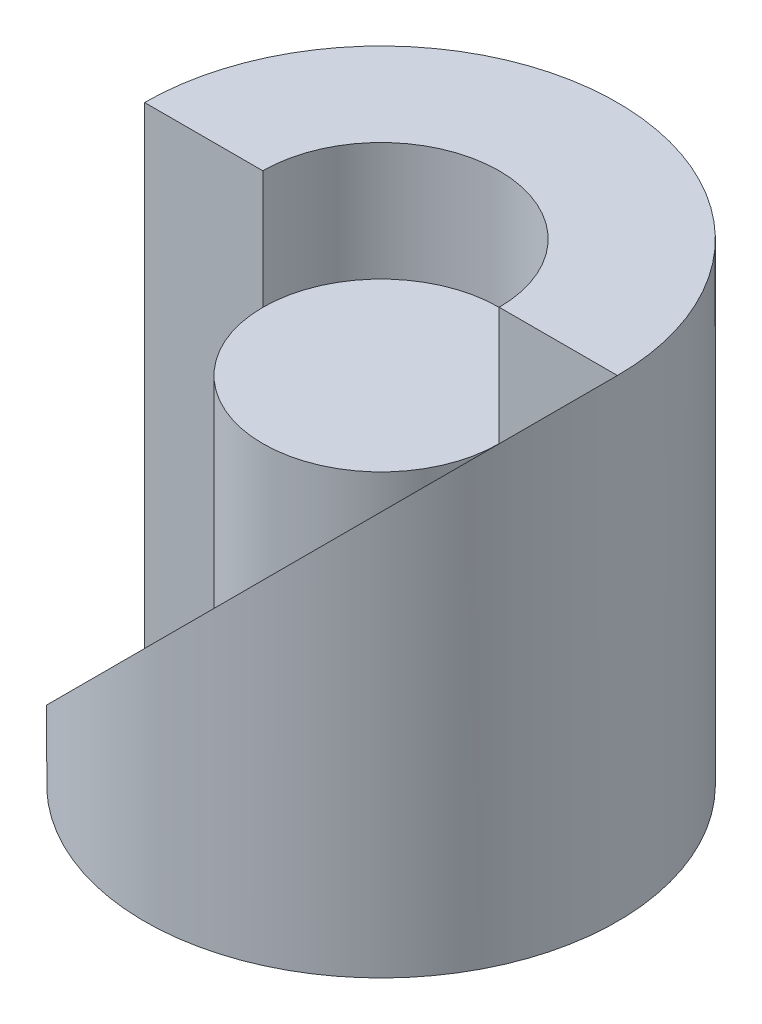
SolidWorks part; units mm, degrees
ref_plane "Front Plane" through (0, 0, 0) normal (0, 0, 1) x (1, 0, 0)
ref_plane "Top Plane" through (0, 0, 0) normal (0, 1, 0) x (1, 0, 0)
ref_plane "Right Plane" through (0, 0, 0) normal (1, 0, 0) x (0, 0, -1)
sketch "Sketch1" plane through (0, 0, 0) normal (0, 1, 0) x (1, 0, 0)
  circle A0 centre (0, 0) radius 20
  circle A1 centre (0, 0) radius 10
extrude "Boss-Extrude3" add sketch "Sketch1" along normal blind 40
sketch "Sketch4" plane through (0, 0, 0) normal (0, 0, 1) x (1, 0, 0)
  line L0 (-20, 0) -> (20, 40)
  line L1 (20, 40) -> (-20, 40)
  line L2 (-20, 40) -> (-20, 0)
extrude "Cut-Extrude2" cut sketch "Sketch4" along normal blind 40
sketch "Sketch5" plane through (0, 0, 0) normal (0, 1, 0) x (1, 0, 0)
  circle A0 centre (0, 0) radius 9.9926
extrude "Boss-Extrude4" add sketch "Sketch5" along normal blind 30 separate body
